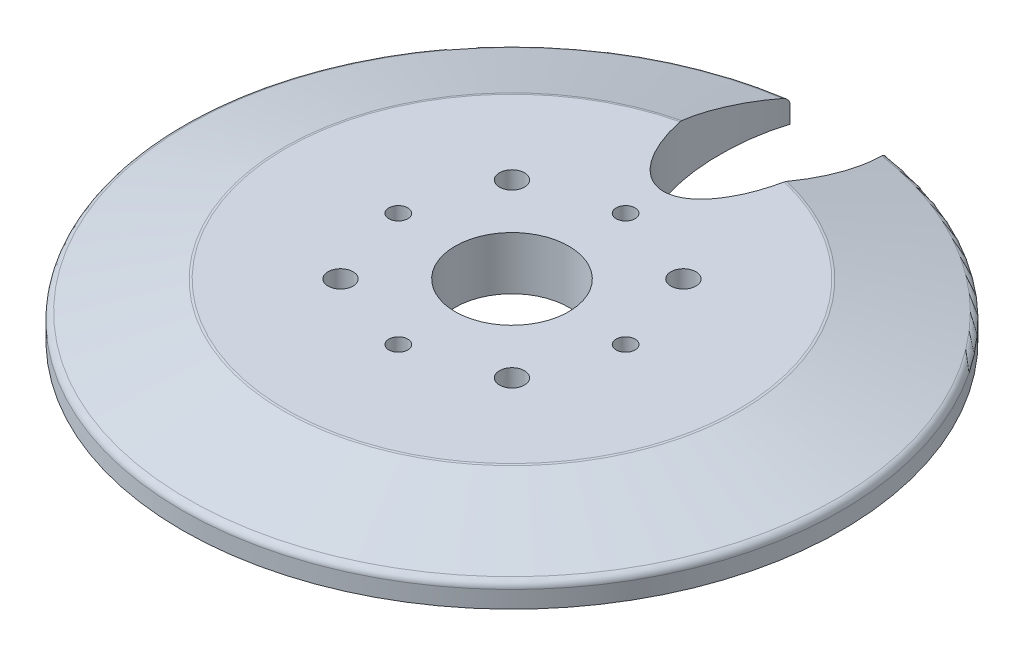
SolidWorks part; units mm, degrees
material "3.1355 (EN-AW 2024)"
ref_plane "Front" through (0, 0, 0) normal (0, 0, 1) x (1, 0, 0)
ref_plane "Top" through (0, 0, 0) normal (0, 1, 0) x (1, 0, 0)
ref_plane "Right" through (0, 0, 0) normal (1, 0, 0) x (0, 0, -1)
sketch "Эскиз1" plane through (0, 0, 0) normal (0, 0, 1) x (1, 0, 0)
  line L0 (0, 0) -> (-43.5, 0)
  line L1 (-43.5, 0) -> (-43.5, 3)
  line L2 (-43.5, 3) -> (-30, 7)
  line L3 (-30, 7) -> (0, 7)
  line L4 (0, 7) -> (0, 0)
  dimension "D1" = 43.5
  dimension "D2" = 3
  dimension "D3" = 30
  dimension "D4" = 7
revolve "Повернуть1" add sketch "Эскиз1" angle 360 about L4
sketch "Эскиз2" plane through (0, 7, 0) normal (0, 1, 0) x (1, 0, 0)
  circle A0 centre (0, 0) radius 7.5
  dimension "D1" = 15
extrude "Вырез-Вытянуть1" cut sketch "Эскиз2" against normal through all
sketch "Эскиз3" plane through (0, 7, 0) normal (0, 1, 0) x (1, 0, 0)
  line L0 (0, 0) -> (0, 20) construction
  ellipse E0 centre (0, 35) end of major axis (0, 20) minor radius 7.5
  dimension "D1" = 20
  dimension "D2" = 7.5
  dimension "D3" = 15
extrude "Вырез-Вытянуть2" cut sketch "Эскиз3" against normal through all
sketch "Эскиз4" plane through (0, 7, 0) normal (0, 1, 0) x (1, 0, 0)
  circle A0 centre (0, 0) radius 15 construction
  point P3 (0, 15)
  point P4 (15, 0)
  point P5 (0, -15)
  point P6 (-15, 0)
  dimension "D1" = 30
hole_wizard "Отверстие обработанное метчиком M3x0.51" positions "Эскиз6" profile "Эскиз5" tap size "M3x0.5" standard "Ansi Metric" end condition through all
sketch "Эскиз6" plane through (0, 7, 0) normal (0, 1, 0) x (1, 0, 0)
  point P0 (0, 15)
  point P3 (-15, 0)
  point P6 (0, -15)
  point P9 (15, 0)
sketch "Эскиз5" plane through (0, 7, -15) normal (1, 0, 0) x (0, 0, 1)
  line L0 (0, 0) -> (0, 7)
  line L1 (0, 7) -> (1.25, 7)
  line L2 (1.25, 7) -> (1.25, 0)
  line L5 (1.25, 0) -> (0, 0)
  line L11 (0, -6.35) -> (0, 107.95) construction
  dimension "Диаметр проходного сверла" = 2.5
  dimension "Глубина проходного сверла" = 7
cosmetic thread "Отверстие резьбы1"
cosmetic thread "Отверстие резьбы2"
cosmetic thread "Отверстие резьбы3"
cosmetic thread "Отверстие резьбы4"
sketch "Эскиз7" plane through (0, 7, 0) normal (0, 1, 0) x (1, 0, 0)
  line L0 (0, 0) -> (-11.3137, 11.3137) construction
  line L1 (0, 0) -> (-16, 0) construction
  line L2 (0, 0) -> (11.3137, 11.3137) construction
  line L3 (0, 0) -> (11.3137, -11.3137) construction
  line L4 (0, 0) -> (-11.3137, -11.3137) construction
  circle A0 centre (0, 0) radius 16 construction
  point P11 (0, 0)
  dimension "D1" = 32
  dimension "D2" = 45
  dimension "D3" = 4
hole_wizard "Отверстие обработанное метчиком M4x0.71" positions "Эскиз9" profile "Эскиз8" tap size "M4x0.7" standard "Ansi Metric" end condition through all
sketch "Эскиз9" plane through (0, 7, 0) normal (0, 1, 0) x (1, 0, 0)
  point P0 (-11.3137, 11.3137)
  point P3 (11.3137, 11.3137)
  point P6 (11.3137, -11.3137)
  point P9 (-11.3137, -11.3137)
sketch "Эскиз8" plane through (-11.3137, 7, -11.3137) normal (1, 0, 0) x (0, 0, 1)
  line L0 (0, 0) -> (0, 7)
  line L1 (0, 7) -> (1.65, 7)
  line L2 (1.65, 7) -> (1.65, 0)
  line L5 (1.65, 0) -> (0, 0)
  line L11 (0, -6.35) -> (0, 107.95) construction
  dimension "Диаметр проходного сверла" = 3.3
  dimension "Глубина проходного сверла" = 7
cosmetic thread "Отверстие резьбы5"
cosmetic thread "Отверстие резьбы6"
cosmetic thread "Отверстие резьбы7"
cosmetic thread "Отверстие резьбы8"
fillet "Скругление1" radius 1 2 edges at (0, 7, 30) (0, 3, 43.5)
